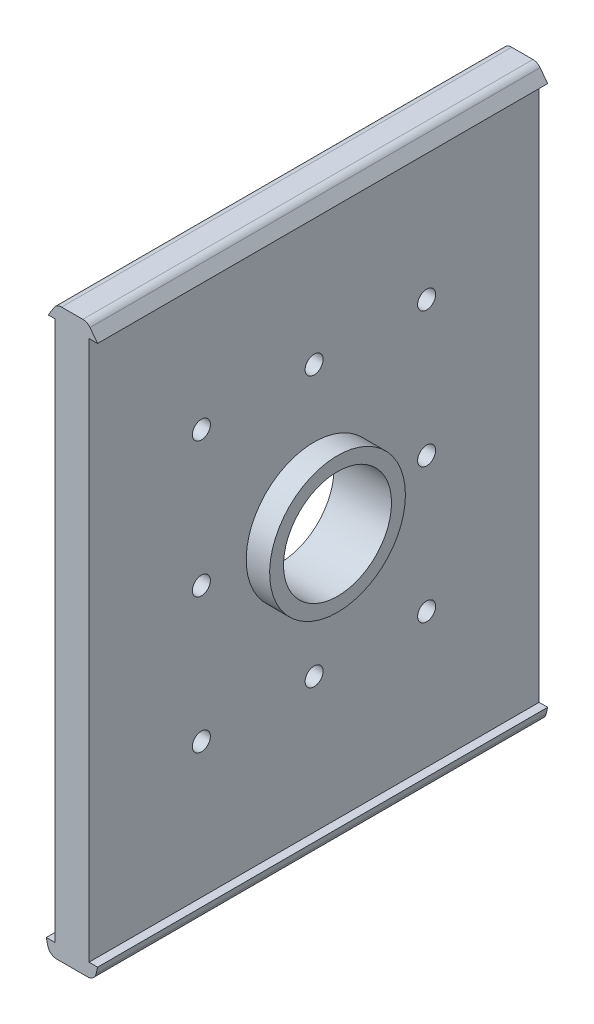
SolidWorks part; units mm, degrees
ref_plane "Plano frontal" through (0, 0, 0) normal (0, 0, 1) x (1, 0, 0)
ref_plane "Plano superior" through (0, 0, 0) normal (0, 1, 0) x (1, 0, 0)
ref_plane "Plano direito" through (0, 0, 0) normal (1, 0, 0) x (0, 0, -1)
sketch "Esboço1" plane through (0, 0, 0) normal (0, 0, 1) x (1, 0, 0)
  line L0 (0, 0) -> (0, 14.1176) construction
  line L1 (-3.8, -98.1786) -> (-5.7, -98.1786)
  line L2 (0, -101.1786) -> (0, -98.1786) construction
  line L3 (0, -98.1786) -> (-3.8, -98.1786) construction
  line L4 (-3.4129, -101.1786) -> (3.4129, -101.1786)
  line L5 (3.8, -98.1786) -> (0, -98.1786) construction
  line L6 (5.7, -98.1786) -> (5.7, -30.5351) construction
  line L7 (-5.3606, -99.6331) -> (-5.7, -98.1786)
  line L8 (5.7, -98.1786) -> (5.3606, -99.6331)
  line L9 (5.7, -30.5351) -> (5.7, 21.8214) construction
  line L10 (5.7, 21.8214) -> (3.4129, 21.8214) construction
  line L11 (3.8, -98.1786) -> (3.8, 21.8214)
  line L12 (3.8, 21.8214) -> (3.4129, 21.8214)
  line L13 (-3.8, -98.1786) -> (-3.8, 21.8214)
  line L14 (3.8, -98.1786) -> (5.7, -98.1786)
  line L15 (-5.2668, 21.8214) -> (-5.2668, 17.6583) construction
  line L16 (3.4129, -101.1786) -> (3.4129, 21.8214) construction
  line L17 (-3.4129, -101.1786) -> (-3.4129, 24.8214) construction
  line L18 (5.7, 21.8214) -> (3.4129, 21.8214)
  line L19 (3.4129, 21.8214) -> (3.4129, 24.8214) construction
  line L20 (5.7, 21.8214) -> (4.0133, 24.0339)
  line L21 (2.4227, 24.8214) -> (-2.2978, 24.8214)
  line L22 (-3.9992, 23.8727) -> (-5.2668, 21.8214)
  line L23 (-3.4129, 21.8214) -> (-5.2668, 21.8214) construction
  line L24 (-3.4129, 21.8214) -> (-3.8, 21.8214)
  line L25 (-3.4129, 21.8214) -> (-5.2668, 21.8214)
  arc A0 (3.4129, -101.1786) -> (5.3606, -99.6331) centre (3.4129, -99.1786) ccw
  arc A1 (-5.3606, -99.6331) -> (-3.4129, -101.1786) centre (-3.4129, -99.1786) ccw
  arc A2 (-2.2978, 24.8214) -> (-3.9992, 23.8727) centre (-2.2978, 22.8214) ccw
  arc A3 (2.4227, 24.8214) -> (4.0133, 24.0339) centre (2.4227, 22.8214) cw
  point P15 (5, -101.1786)
  point P18 (-5, -101.1786)
  dimension "D9" = 2
  dimension "D11" = 2
  dimension "D1" = 5.7
  dimension "D2" = 5.7
  dimension "D3" = 11.4
  dimension "D4" = 5.7
  dimension "D5" = 5
  dimension "D6" = 7.6
  dimension "D7" = 3.8
  dimension "D8" = 120
  dimension "D10" = 3
  dimension "D12" = 3
extrude "Ressalto-extrusão1" add sketch "Esboço1" along normal blind 160
sketch "Esboço2" plane through (0, 0, 0) normal (0, 0, 1) x (1, 0, 0)
  line L1 (-3.8, 21.8214) -> (3.8, 21.8214)
  line L2 (-3.8, 21.8214) -> (-3.8, -98.1786)
  line L3 (-3.8, -98.1786) -> (3.8, -98.1786)
  line L4 (3.8, 21.8214) -> (3.8, -98.1786)
extrude "Corte-extrusão1" cut sketch "Esboço2" along normal blind 30
sketch3d "3DSketch2"
  line L1 (-3.8, 21.8214, 160) -> (3.8, 21.8214, 160)
  line L2 (-3.8, 21.8214, 160) -> (-3.8, -98.1786, 160)
  line L3 (-3.8, -98.1786, 160) -> (3.8, -98.1786, 160)
  line L4 (3.8, 21.8214, 160) -> (3.8, -98.1786, 160)
  dimension "D1" = 160
extrude "Corte-extrusão2" cut sketch "3DSketch2" along direction (0, 0, 1) on the side of the normal blind 30
sketch3d "3DSketch3"
  line L0 (3.8, 21.8214, 130) -> (3.8, 21.8214, 80) construction
  line L1 (3.8, 21.8214, 130) -> (3.8, 21.8214, 30) construction
  line L2 (3.8, 21.8214, 80) -> (3.8, -98.1786, 80) construction
  line L3 (3.8, -98.1786, 130) -> (3.8, -98.1786, 30) construction
  line L4 (3.8, -98.1786, 80) -> (3.8, -98.1786, 130) construction
  line L5 (3.8, -98.1786, 130) -> (3.8, -38.1786, 130) construction
  line L6 (3.8, -98.1786, 130) -> (3.8, 21.8214, 130) construction
  line L7 (3.8, -38.1786, 130) -> (3.8, -38.1786, 30) construction
  line L8 (3.8, -98.1786, 30) -> (3.8, 21.8214, 30) construction
  line L9 (3.8, 21.8214, 130) -> (3.8, -98.1786, 30) construction
  line L10 (3.8, -98.1786, 30) -> (3.8, -98.1786, 130) construction
  line L11 (3.8, -98.1786, 130) -> (3.8, 21.8214, 30) construction
  line L12 (3.8, 21.8214, 30) -> (3.8, -38.1786, 130) construction
  line L13 (3.8, -38.1786, 130) -> (3.8, 21.8214, 130) construction
  line L14 (3.8, 21.8214, 130) -> (3.8, -38.1786, 30) construction
  line L15 (3.8, -38.1786, 30) -> (3.8, -8.1786, 30) construction
  line L16 (3.8, -8.1786, 30) -> (3.8, -8.1786, 130) construction
  line L17 (3.8, -38.1786, 130) -> (3.8, -98.1786, 30) construction
  line L18 (3.8, -98.1786, 30) -> (3.8, -98.1786, 130) construction
  line L19 (3.8, -98.1786, 130) -> (3.8, -38.1786, 30) construction
  line L20 (3.8, -68.1786, 80) -> (3.8, -68.1786, 30) construction
  line L21 (3.8, -68.1786, 30) -> (3.8, -68.1786, 130) construction
  line L22 (3.8, 21.8214, 105) -> (3.8, -98.1786, 80) construction
  line L23 (3.8, -98.1786, 80) -> (3.8, -98.1786, 105) construction
  line L24 (3.8, -98.1786, 105) -> (3.8, 21.8214, 80) construction
  line L25 (3.8, 21.8214, 80) -> (3.8, -98.1786, 55) construction
  line L26 (3.8, -98.1786, 55) -> (3.8, 21.8214, 55) construction
  line L27 (3.8, 21.8214, 55) -> (3.8, -98.1786, 80) construction
  line L28 (3.8, -98.1786, 80) -> (3.8, -38.1786, 67.5) construction
  line L29 (3.8, -38.1786, 67.5) -> (3.8, -98.1786, 67.5) construction
  line L30 (3.8, -98.1786, 67.5) -> (3.8, 21.8214, 67.5) construction
  line L31 (3.8, -38.1786, 92.5213) -> (3.8, 21.8214, 92.5213) construction
  line L32 (3.8, 21.8214, 92.5213) -> (3.8, -98.1786, 92.5213) construction
  circle A0 centre (3.8, -38.1786, 80) radius 2
  circle A1 centre (3.8, -8.1786, 80) radius 2
  circle A2 centre (3.8, -68.1786, 80) radius 2
  circle A3 centre (3.8, -68.1786, 55) radius 2
  circle A4 centre (3.8, -38.1786, 55) radius 2
  circle A5 centre (3.8, -8.1786, 55) radius 2
  circle A6 centre (3.8, -68.1786, 105.0426) radius 2
  circle A7 centre (3.8, -38.1786, 105.0426) radius 2
  circle A8 centre (3.8, -8.1786, 105.0426) radius 2
  point P18 (5.8, -38.1786, 80)
  point P27 (5.8, -8.1786, 80)
  point P32 (5.8, -68.1786, 80)
  point P42 (5.8, -68.1786, 55)
  point P45 (5.8, -38.1786, 55)
  point P48 (5.8, -8.1786, 55)
  point P54 (5.8, -68.1786, 105.0426)
  point P57 (5.8, -38.1786, 105.0426)
  point P60 (5.8, -8.1786, 105.0426)
extrude "Corte-extrusão3" cut sketch "3DSketch3" along direction (-1, 0, 0) on the side against the normal blind 70
sketch "Esboço3" plane through (0, 0, 0) normal (1, 0, 0) x (0, 0, -1)
  line L0 (-130, 21.8214) -> (-130, 24.8214) construction
  line L1 (-160, 24.8214) -> (0, 24.8214) construction
  line L2 (-130, 24.8214) -> (-30, 21.8214) construction
  line L3 (-30, 21.8214) -> (-30, 24.8214) construction
  line L4 (-30, -98.1786) -> (-30, -101.1786) construction
  line L5 (-160, -101.1786) -> (0, -101.1786) construction
  line L6 (-30, -101.1786) -> (-130, -98.1786) construction
  line L7 (-130, -98.1786) -> (-130, -101.1786) construction
  line L9 (-30, 24.8214) -> (15.0153, 24.8214)
  line L10 (-30, 24.8214) -> (-30, -104.6572)
  line L11 (-30, -104.6572) -> (15.0153, -104.6572)
  line L12 (15.0153, 24.8214) -> (15.0153, -104.6572)
  line L13 (-130, 24.8214) -> (-167.1926, 24.8214)
  line L14 (-130, 24.8214) -> (-130, -104.6572)
  line L15 (-130, -104.6572) -> (-167.1926, -104.6572)
  line L16 (-167.1926, 24.8214) -> (-167.1926, -104.6572)
extrude "Corte-extrusão4" cut sketch "Esboço3" along normal blind 31.5103 and the other way blind 38
sketch "Esboço4" plane through (0, 0, 0) normal (1, 0, 0) x (0, 0, -1)
  circle A0 centre (-80, -38.1786) radius 12
  dimension "D1" = 24
extrude "Corte-extrusão5" cut sketch "Esboço4" along normal blind 52.5103 and the other way blind 54
sketch "Esboço5" plane through (0, 0, 0) normal (1, 0, 0) x (0, 0, -1)
  circle A0 centre (-80, -38.1786) radius 12
  circle A1 centre (-80, -38.1786) radius 15.0847
extrude "Ressalto-extrusão3" add sketch "Esboço5" along normal blind 9
